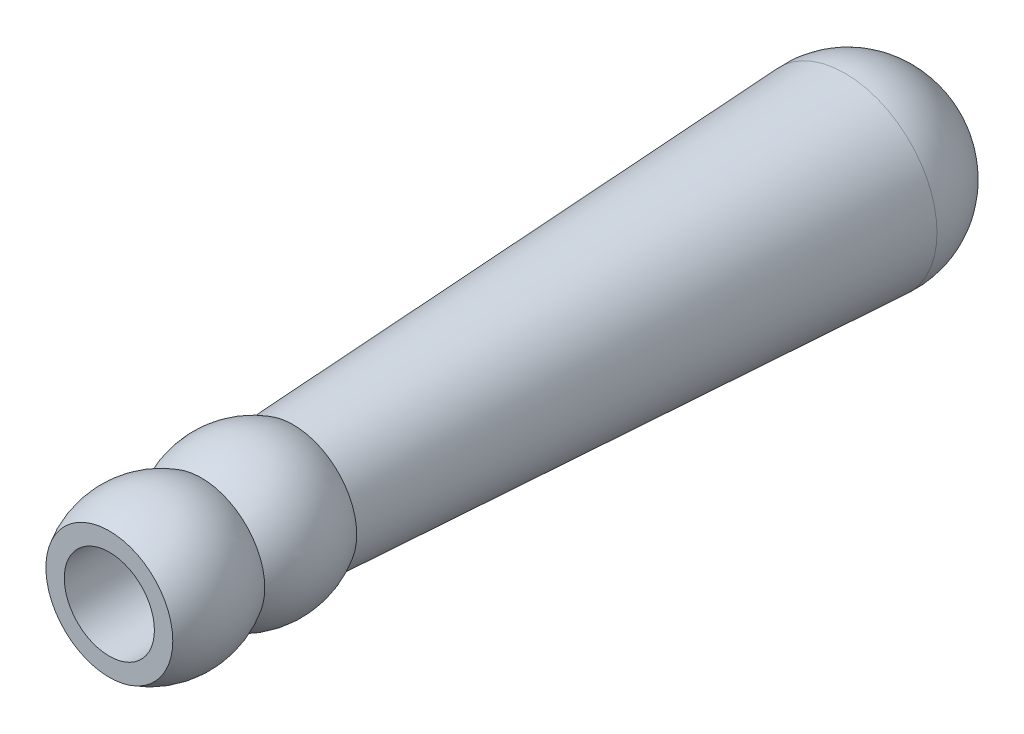
SolidWorks part; units mm, degrees
ref_plane "Front Plane" through (0, 0, 0) normal (0, 0, 1) x (1, 0, 0)
ref_plane "Top Plane" through (0, 0, 0) normal (0, 1, 0) x (1, 0, 0)
ref_plane "Right Plane" through (0, 0, 0) normal (1, 0, 0) x (0, 0, -1)
sketch "Sketch1" plane through (0, 0, 0) normal (0, 1, 0) x (1, 0, 0)
  line L0 (0, -810.6611) -> (0, 39722.3921) construction
  line L1 (6.223, -813.5287) -> (6.223, 39719.5245) construction
  line L2 (6.223, 0) -> (8.763, 0)
  line L3 (6.223, 0) -> (6.223, 19.05)
  line L4 (-995.9876, 101.6) -> (49004.0124, 101.6) construction
  line L5 (8.763, 25.4) -> (12.7, 101.6)
  line L6 (-19.05, -945.3414) -> (-19.05, 49054.6586) construction
  line L7 (6.223, 19.05) -> (0, 19.05)
  line L8 (0, 114.3) -> (0, 19.05)
  line L9 (0, 19.05) -> (-0.0274, 19.0194)
  arc A0 (8.763, 0) -> (8.763, 12.7) centre (-1.7475, 6.35) ccw
  arc A1 (8.763, 12.7) -> (8.763, 25.4) centre (-1.7475, 19.05) ccw
  arc A2 (12.7, 101.6) -> (0, 114.3) centre (0.6751, 102.2751) ccw
  dimension "D1" = 6.223
  dimension "D2" = 19.05
  dimension "D3" = 2.54
  dimension "D4" = 101.6
  dimension "D5" = 12.7
  dimension "D6" = 12.7
  dimension "D7" = 19.05
  dimension "D8" = 12.7
revolve "Revolve1" add sketch "Sketch1" angle 360 about L0
